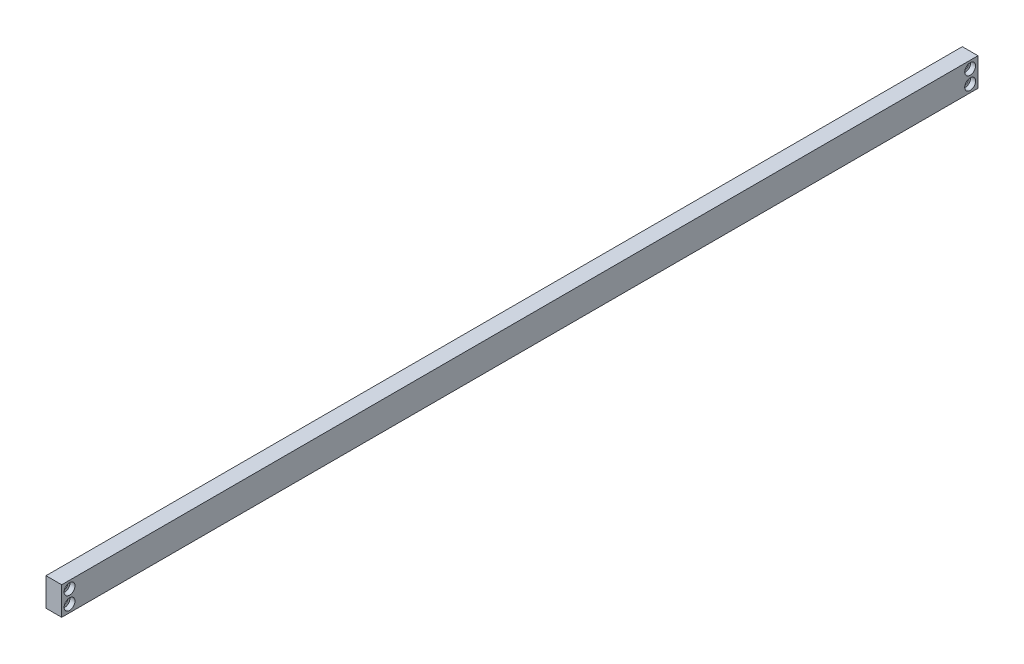
SolidWorks part; units mm, degrees
material "1060 Alloy"
ref_plane "Front Plane" through (0, 0, 0) normal (0, 0, 1) x (1, 0, 0)
ref_plane "Top Plane" through (0, 0, 0) normal (0, 1, 0) x (1, 0, 0)
ref_plane "Right Plane" through (0, 0, 0) normal (1, 0, 0) x (0, 0, -1)
sketch "Sketch1" plane through (0, 0, 0) normal (0, 0, 1) x (1, 0, 0)
  line L1 (0, 0) -> (6.35, 0)
  line L2 (0, 0) -> (0, 11.43)
  line L3 (0, 11.43) -> (6.35, 11.43)
  line L4 (6.35, 0) -> (6.35, 11.43)
  dimension "D1" = 6.35
  dimension "D2" = 11.43
extrude "Boss-Extrude1" add sketch "Sketch1" against normal blind 370.84
hole_wizard "M2x0.4 Tapped Hole1" [suppressed] positions "Sketch2" profile "Sketch3" tap size "M2x0.4" standard "ANSI Metric"
sketch "Sketch2" plane through (0, 0, 0) normal (0, 0, 1) x (1, 0, 0)
  line L8 (0, 5.715) -> (6.35, 5.715) construction
  line L9 (0, 11.43) -> (0, 0) construction
  line L10 (6.35, 0) -> (6.35, 11.43) construction
  line L12 (3.175, 2.54) -> (3.175, 8.89) construction
  point P0 (3.175, 2.54)
  point P2 (3.175, 8.89)
  point P34 (3.175, 5.715)
  dimension "D1" = 6.35
sketch "Sketch3" plane through (3.175, 2.54, 0) normal (1, 0, 0) x (0, -1, 0)
  line L0 (0, 0) -> (0, 13.1807)
  line L1 (0, 13.1807) -> (0.8, 12.7)
  line L2 (0.8, 12.7) -> (0.8, 0)
  line L5 (0.8, 0) -> (0, 0)
  line L10 (0, 13.1807) -> (-0.8, 12.7) construction
  line L11 (0, -6.35) -> (0, 107.95) construction
  dimension "Tap Drill Dia." = 1.6
  dimension "Tap Drill Depth" = 12.7
  dimension "Drill Angle" = 118
cosmetic thread "Hole Thread1" [suppressed] parameters "D1"=4.064, "D2"=2
cosmetic thread "Hole Thread2" [suppressed] parameters "D1"=4.064, "D2"=2
ref_plane "Plane1" through (0, 0, -185.42) normal (0, 0, 1) x (1, 0, 0)
mirror "Mirror1" [suppressed] about plane through (0, 0, -185.42) normal (0, 0, 1)
cosmetic thread "Hole Thread3" [suppressed] parameters "D1"=4.064, "D2"=2
cosmetic thread "Hole Thread4" [suppressed] parameters "D1"=4.064, "D2"=2
sketch "Sketch4" plane through (6.35, 0, 0) normal (1, 0, 0) x (0, 0, -1)
  line L0 (3.175, 11.43) -> (3.175, 0) construction
  line L1 (370.84, 11.43) -> (0, 11.43) construction
  line L2 (370.84, 0) -> (0, 0) construction
  line L3 (0, 0) -> (0, 11.43) construction
  point P8 (3.175, 8.382)
  point P9 (3.175, 3.048)
  dimension "D1" = 3.175
  dimension "D2" = 3.048
  dimension "D3" = 3.048
hole_wizard "CBORE for M2 SHCS2" positions "Sketch5" profile "Sketch6" counterbore size "M2" standard "ANSI Metric" end condition through all
sketch "Sketch5" plane through (6.35, 0, 0) normal (1, 0, 0) x (0, 0, -1)
  point P0 (3.175, 8.382)
  point P3 (3.175, 3.048)
sketch "Sketch6" plane through (6.35, 8.382, -3.175) normal (0, 1, 0) x (0, 0, -1)
  line L0 (0, 0) -> (0, 6.35)
  line L1 (0, 6.35) -> (1.2, 6.35)
  line L3 (1.2, 6.35) -> (1.2, 2)
  line L4 (1.2, 2) -> (2.2, 2)
  line L5 (2.2, 2) -> (2.2, 0)
  line L7 (2.2, 0) -> (0, 0)
  line L11 (0, -6.35) -> (0, 107.95) construction
  dimension "Thru Hole Dia." = 2.4
  dimension "Thru Hole Depth" = 6.35
  dimension "C'Bore Dia." = 4.4
  dimension "C'Bore Depth" = 2
ref_plane "Plane2" through (0, 0, -185.42) normal (0, 0, 1) x (1, 0, 0)
mirror "Mirror2" about plane through (0, 0, -185.42) normal (0, 0, 1) of "CBORE for M2 SHCS2"
